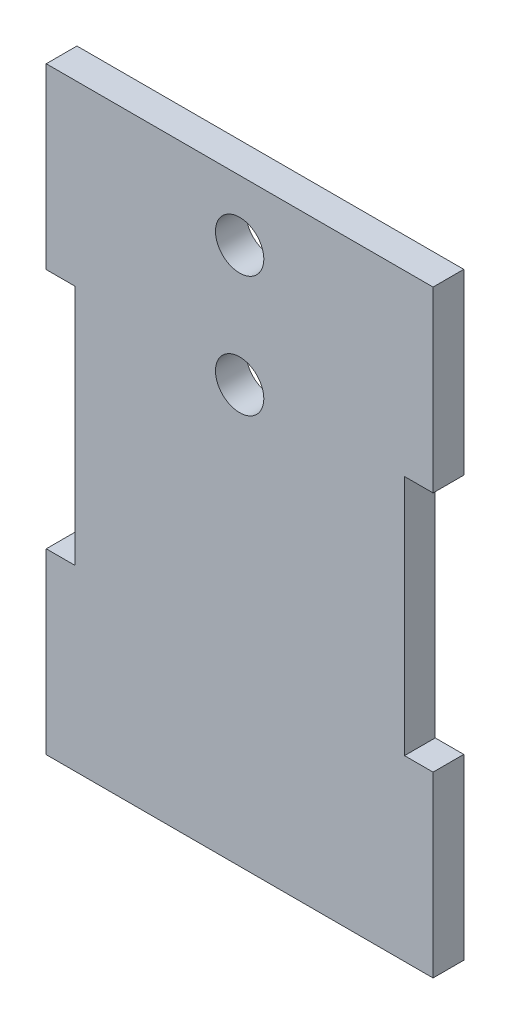
SolidWorks part; units mm, degrees
ref_plane "Front Plane" through (0, 0, 0) normal (0, 0, 1) x (1, 0, 0)
ref_plane "Top Plane" through (0, 0, 0) normal (0, 1, 0) x (1, 0, 0)
ref_plane "Right Plane" through (0, 0, 0) normal (1, 0, 0) x (0, 0, -1)
sketch "Sketch1" plane through (0, 0, 0) normal (0, 0, 1) x (1, 0, 0)
  line L0 (-14.82, 10) -> (-14.82, 24.75) construction
  line L1 (-16, -24.75) -> (16, -24.75)
  line L2 (-16, -24.75) -> (-16, -10)
  line L3 (-16, 24.75) -> (16, 24.75)
  line L4 (16, -24.75) -> (16, -10)
  line L5 (-16, -24.75) -> (16, 24.75) construction
  line L6 (-16, 24.75) -> (16, -24.75) construction
  line L7 (-16, 10) -> (-13.64, 10)
  line L9 (-16, -10) -> (-13.64, -10)
  line L10 (-13.64, 10) -> (-13.64, -10)
  line L11 (-14.82, -10) -> (-14.82, -24.75) construction
  line L13 (0, -55) -> (0, 55) construction
  line L14 (16, -10) -> (13.64, -10)
  line L15 (13.64, 10) -> (13.64, -10)
  line L16 (16, 10) -> (13.64, 10)
  line L18 (-16, 10) -> (-16, 24.75)
  line L19 (16, 10) -> (16, 24.75)
  circle A0 centre (0, 9.75) radius 2
  circle A1 centre (0, 19.75) radius 2
  point P0 (0, 0)
  dimension "D5" = 4
  dimension "D1" = 32
  dimension "D2" = 49.5
  dimension "D3" = 2.36
  dimension "D4" = 20
  dimension "D6" = 5
  dimension "D7" = 10
extrude "Boss-Extrude1" add sketch "Sketch1" along normal blind 2.54
